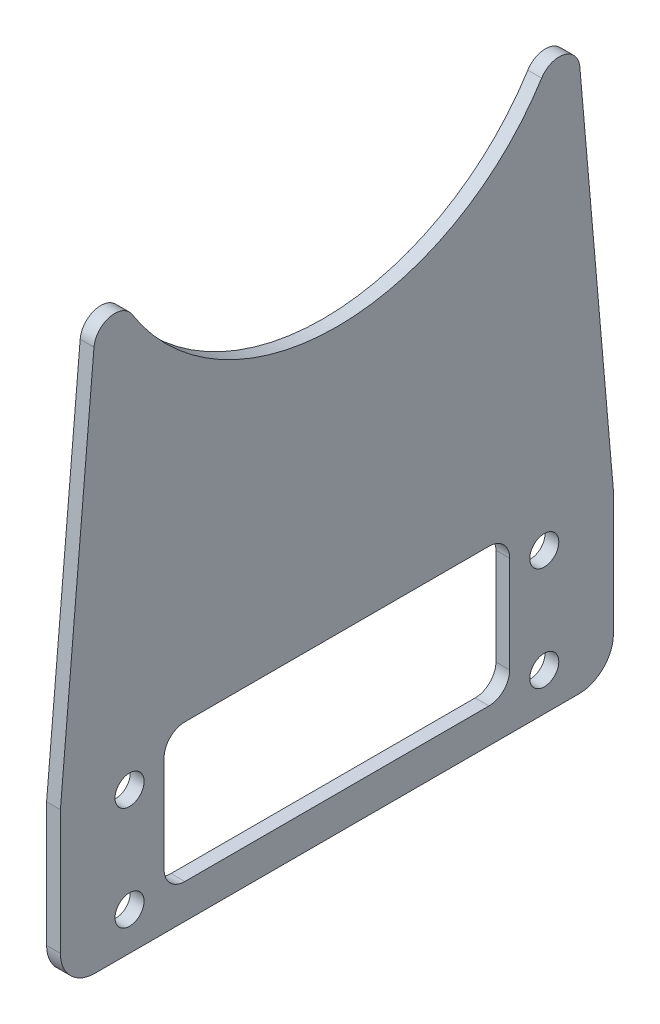
SolidWorks part; units mm, degrees
material "Thornel Mat VMA"
ref_plane "前视基准面" through (0, 0, 0) normal (0, 0, 1) x (1, 0, 0)
ref_plane "上视基准面" through (0, 0, 0) normal (0, 1, 0) x (1, 0, 0)
ref_plane "右视基准面" through (0, 0, 0) normal (1, 0, 0) x (0, 0, -1)
sketch "草图1" plane through (0, 0, 0) normal (1, 0, 0) x (0, 0, -1)
  line L0 (-40, 11.5) -> (-34.0888, 79.0656)
  line L7 (-40, 11.5) -> (40, 11.5) construction
  line L8 (-40, 11.5) -> (-40, -11.5)
  line L9 (-40, -11.5) -> (40, -11.5)
  line L10 (40, 11.5) -> (40, -11.5)
  line L11 (-40, 11.5) -> (40, -11.5) construction
  line L12 (-40, -11.5) -> (40, 11.5) construction
  line L14 (34.0888, 79.0656) -> (40, 11.5)
  arc A4 (-34.0888, 79.0656) -> (34.0888, 79.0656) centre (0, 87) ccw
  point P6 (0, 0)
  dimension "D7" = 35
  dimension "D3" = 80
  dimension "D4" = 23
  dimension "D6" = 98.5
  dimension "D8" = 85
extrude "凸台-拉伸1" add sketch "草图1" along normal blind 2
sketch "草图2" plane through (2, 0, 0) normal (1, 0, 0) x (0, 0, -1)
  line L0 (-40, -11.5) -> (40, -11.5) construction
  line L1 (-25, 13.5) -> (25, 13.5)
  line L2 (-25, 13.5) -> (-25, -6.5)
  line L3 (-25, -6.5) -> (25, -6.5)
  line L4 (25, 13.5) -> (25, -6.5)
  line L5 (-25, 13.5) -> (25, -6.5) construction
  line L6 (-25, -6.5) -> (25, 13.5) construction
  line L8 (-30, 9) -> (30, 9) construction
  line L9 (-30, 9) -> (-30, -6) construction
  line L10 (-30, -6) -> (30, -6) construction
  line L11 (30, 9) -> (30, -6) construction
  line L12 (-30, 9) -> (30, -6) construction
  line L13 (-30, -6) -> (30, 9) construction
  circle A0 centre (-30, 9) radius 2.1
  circle A1 centre (-30, -6) radius 2.1
  circle A2 centre (30, -6) radius 2.1
  circle A3 centre (30, 9) radius 2.1
  point P0 (0, 3.5)
  point P5 (0, 3.5)
  point P20 (0, 1.5)
  dimension "D6" = 4.2
  dimension "D1" = 50
  dimension "D2" = 20
  dimension "D3" = 5
  dimension "D4" = 60
  dimension "D5" = 15
  dimension "D7" = 1.5
extrude "切除-拉伸1" cut sketch "草图2" against normal blind 2
fillet "圆角1" radius 3 6 edges at (1, -6.5, 25) (1, 13.5, -25) (1, -6.5, -25) (1, 13.5, 25) (1, 79.0656, -34.0888) (1, 79.0656, 34.0888)
fillet "圆角2" radius 5 2 edges at (1, -11.5, 40) (1, -11.5, -40)
